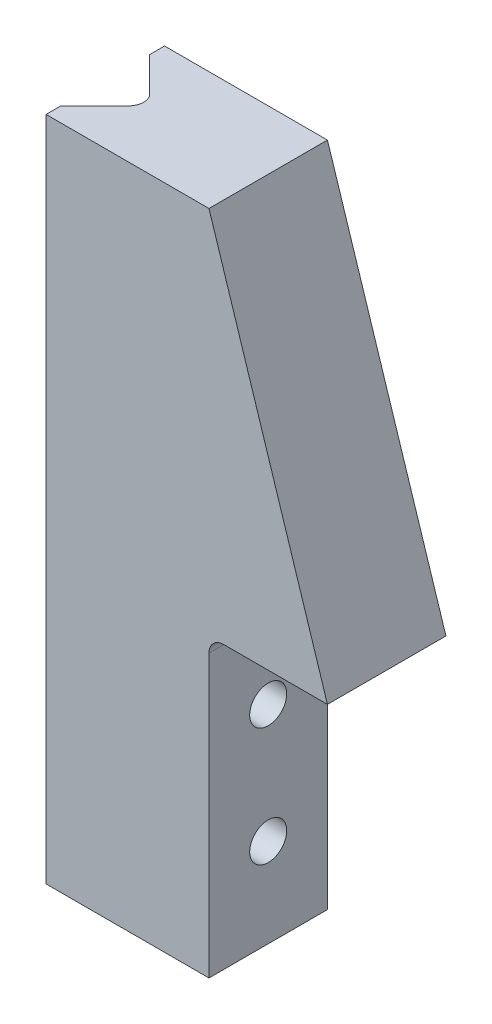
SolidWorks part; units mm, degrees
material "POM Acetal Copolymer"
ref_plane "正面" through (0, 0, 0) normal (0, 0, 1) x (1, 0, 0)
ref_plane "平面" through (0, 0, 0) normal (0, 1, 0) x (1, 0, 0)
ref_plane "右側面" through (0, 0, 0) normal (1, 0, 0) x (0, 0, -1)
sketch "Sketch1" plane through (0, 0, 0) normal (0, 0, 1) x (1, 0, 0)
  line L0 (0, 0) -> (-8, 0)
  line L1 (-8, 0) -> (-8, -20)
  line L2 (-8, -20) -> (-19, -20)
  line L3 (-19, -20) -> (-19, 25)
  line L4 (-19, 25) -> (-8, 25)
  line L5 (-8, 25) -> (0, 0)
  dimension "D1" = 20
  dimension "D2" = 45
extrude "Boss-Extrude1" add sketch "Sketch1" along normal blind 8
sketch "Sketch2" plane through (0, 25, 0) normal (0, 1, 0) x (1, 0, 0)
  line L0 (-19, -4) -> (-19, -1)
  line L1 (-19, -8) -> (-19, 0) construction
  line L2 (-19, -1) -> (-16, -4)
  line L3 (-16, -4) -> (-19, -7)
  line L4 (-19, -7) -> (-19, -4)
extrude "Cut-Extrude1" cut sketch "Sketch2" against normal through all
hole_wizard "M3x0.5 Tapped Hole1" positions "3DSketch1" profile "Sketch3" tap size "M3x0.5" standard "JIS"
sketch3d "3DSketch1"
  line L0 (-8, -20, 8) -> (-8, 0, 8) construction
  line L3 (-8, 0, 8) -> (-8, 0, 0) construction
  point P0 (-8, -6, 4)
  point P2 (-8, -14, 4)
  dimension "D1" = 4
  dimension "D2" = 6
  dimension "D3" = 14
  dimension "D4" = 4
cosmetic thread "Hole Thread1" parameters "D1"=4.6, "D2"=3
cosmetic thread "Hole Thread2" parameters "D1"=4.6, "D2"=3
sketch "Sketch3" plane through (-8, -6, 4) normal (0, 1, 0) x (0, 0, -1)
  line L0 (0, 0) -> (0, 5.7511)
  line L1 (0, 5.7511) -> (1.25, 5)
  line L2 (1.25, 5) -> (1.25, 0)
  line L5 (1.25, 0) -> (0, 0)
  line L10 (0, 5.7511) -> (-1.25, 5) construction
  line L11 (0, -6.35) -> (0, 107.95) construction
  dimension "Tap Drill Dia." = 2.5
  dimension "Tap Drill Depth" = 5
  dimension "Drill Angle" = 118
fillet "Fillet1" radius 1 1 edges at (-16, 2.5, 4)
fillet "Fillet2" radius 1 1 edges at (-8, 0, 4)
